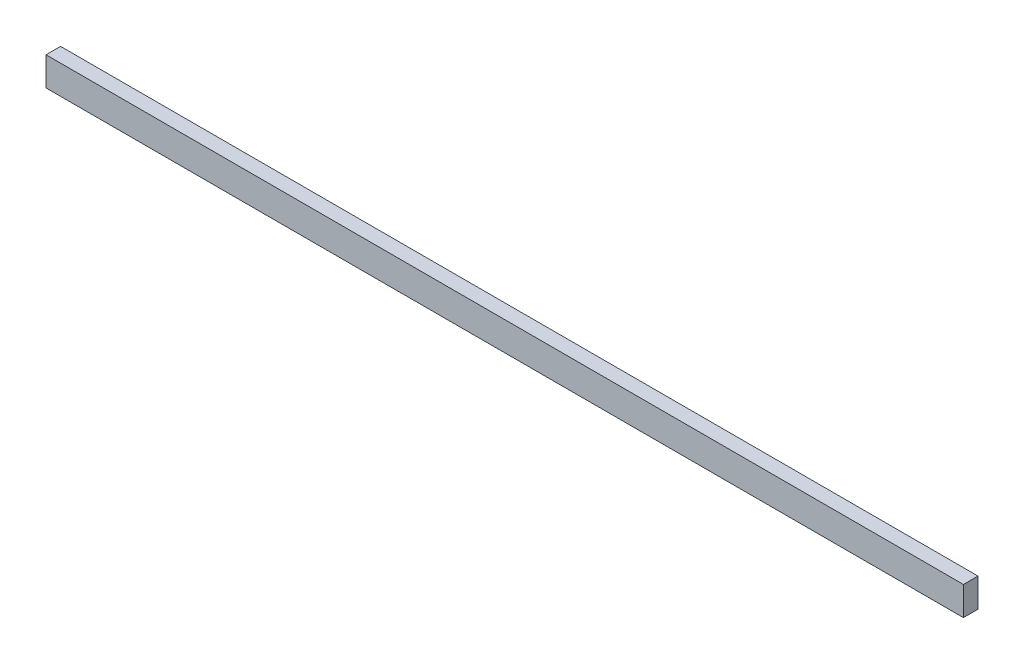
SolidWorks part; units mm, degrees
ref_plane "Front Plane" through (0, 0, 0) normal (0, 0, 1) x (1, 0, 0)
ref_plane "Top Plane" through (0, 0, 0) normal (0, 1, 0) x (1, 0, 0)
ref_plane "Right Plane" through (0, 0, 0) normal (1, 0, 0) x (0, 0, -1)
sketch "Sketch1" plane through (0, 0, 0) normal (1, 0, 0) x (0, 0, -1)
  line L1 (-3.0226, 5.969) -> (3.0226, 5.969)
  line L2 (-3.0226, 5.969) -> (-3.0226, -5.969)
  line L3 (-3.0226, -5.969) -> (3.0226, -5.969)
  line L4 (3.0226, 5.969) -> (3.0226, -5.969)
  line L5 (-3.0226, 5.969) -> (3.0226, -5.969) construction
  line L6 (-3.0226, -5.969) -> (3.0226, 5.969) construction
  point P0 (0, 0)
  dimension "D1" = 11.938
  dimension "D2" = 6.0452
extrude "Boss-Extrude1" add sketch "Sketch1" along normal mid plane 381
